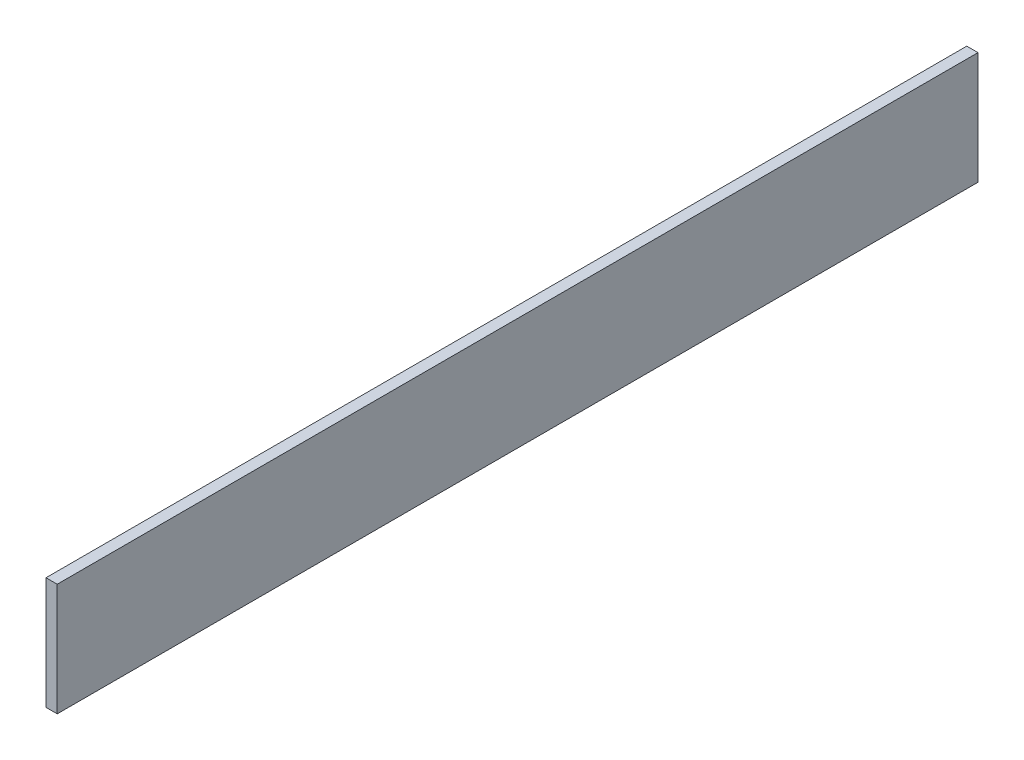
SolidWorks part; units mm, degrees
ref_plane "Front Plane" through (0, 0, 0) normal (0, 0, 1) x (1, 0, 0)
ref_plane "Top Plane" through (0, 0, 0) normal (0, 1, 0) x (1, 0, 0)
ref_plane "Right Plane" through (0, 0, 0) normal (1, 0, 0) x (0, 0, -1)
sketch "Sketch1" plane through (0, 0, 0) normal (0, 0, 1) x (1, 0, 0)
  line L0 (0, 0) -> (0, 50)
  line L1 (0, 50) -> (-5, 50)
  line L2 (-5, 50) -> (-5, 0)
  line L3 (-5, 0) -> (0, 0)
  dimension "D1" = 5
  dimension "D2" = 50
extrude "Boss-Extrude1" add sketch "Sketch1" along normal blind 410
